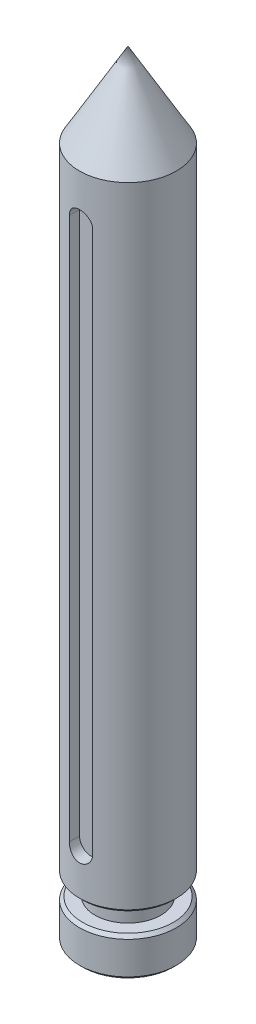
SolidWorks part; units mm, degrees
ref_plane "Alzado" through (0, 0, 0) normal (0, 0, 1) x (1, 0, 0)
ref_plane "Planta" through (0, 0, 0) normal (0, 1, 0) x (1, 0, 0)
ref_plane "Vista lateral" through (0, 0, 0) normal (1, 0, 0) x (0, 0, -1)
sketch "Croquis2" plane through (0, 0, 0) normal (0, 0, 1) x (1, 0, 0)
  line L0 (0, 0) -> (0, 200) construction
  line L1 (0, 0) -> (-12.5, 0)
  line L2 (-12.5, 0) -> (-12.5, 10)
  line L3 (-12.5, 10) -> (-8.5, 10)
  line L4 (-8.5, 10) -> (-8.5, 15)
  line L5 (-8.5, 15) -> (-12.5, 15)
  line L6 (-12.5, 15) -> (-12.5, 178.3)
  line L7 (-12.5, 178.3) -> (0, 200)
  line L8 (0, 200) -> (0, 0)
  line L9 (0, 225.4071) -> (0, 200) construction
  dimension "D1" = 200
  dimension "D2" = 25
  dimension "D3" = 17
  dimension "D4" = 25
  dimension "D5" = 10
  dimension "D6" = 5
  dimension "D7" = 21.7
revolve "Revolución1" add sketch "Croquis2" angle 360 about L8
sketch "Croquis3" plane through (0, 0, 0) normal (0, 0, 1) x (1, 0, 0)
  line L0 (0, 200) -> (0, 0) construction
  line L1 (0, 166.7) -> (0, 26.7) construction
  line L2 (3, 166.7) -> (3, 26.7)
  line L3 (-3, 166.7) -> (-3, 26.7)
  line L4 (-12.5, 0) -> (12.5, 0) construction
  arc A0 (3, 166.7) -> (-3, 166.7) centre (0, 166.7) ccw
  arc A1 (-3, 26.7) -> (3, 26.7) centre (0, 26.7) ccw
  point P6 (0, 96.7)
  dimension "D1" = 6
  dimension "D2" = 26.7
  dimension "D3" = 140
extrude "Cortar-Extruir1" cut sketch "Croquis3" along normal blind 7 from offset 9.5
chamfer "Chaflán1" distance 0.8 angle 45 3 edges at (0, 15, 12.5) (0, 10, 12.5) (0, 0, 12.5)
